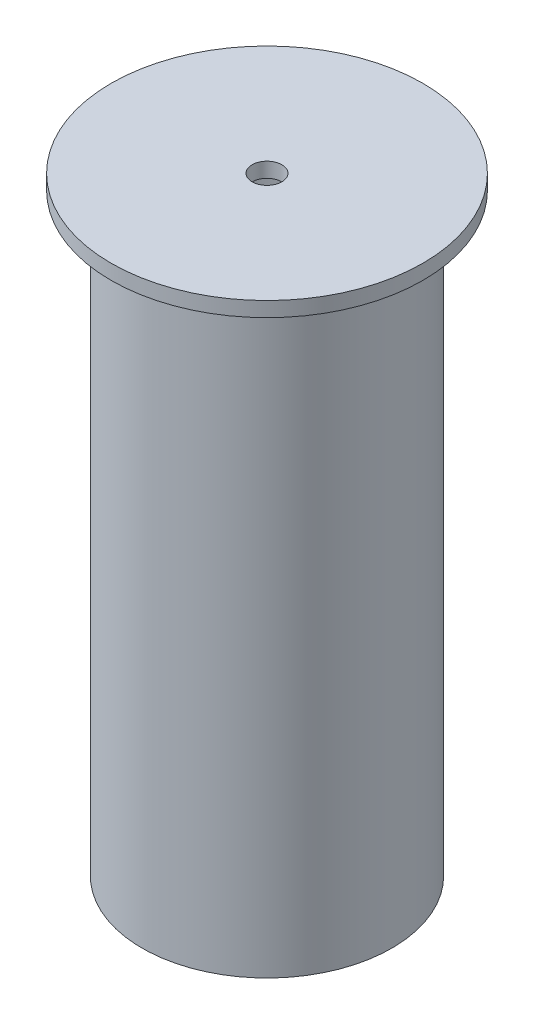
SolidWorks part; units mm, degrees
material "AISI 1020"
ref_plane "Plano frontal" through (0, 0, 0) normal (0, 0, 1) x (1, 0, 0)
ref_plane "Plano superior" through (0, 0, 0) normal (0, 1, 0) x (1, 0, 0)
ref_plane "Plano direito" through (0, 0, 0) normal (1, 0, 0) x (0, 0, -1)
sketch "Esboço1" plane through (0, 0, 0) normal (0, 0, 1) x (1, 0, 0)
  line L0 (0, 0) -> (0, 410) construction
  line L1 (0, 0) -> (215.8131, 0) construction
  line L2 (10, 410) -> (105, 410)
  line L3 (105, 410) -> (105, 400)
  line L4 (84.14, 0) -> (74.74, 0)
  line L5 (74.74, 0) -> (74.74, 10)
  line L6 (74.74, 10) -> (80.74, 10)
  line L7 (80.74, 10) -> (80.74, 400)
  line L8 (80.74, 400) -> (10, 400)
  line L10 (105, 400) -> (84.14, 400)
  line L11 (84.14, 400) -> (84.14, 0)
  line L12 (10, 410) -> (10, 400)
  dimension "D1" = 3.4
  dimension "D2" = 10
  dimension "D3" = 6
  dimension "D4" = 10
  dimension "D5" = 210
  dimension "D6" = 400
  dimension "D7" = 168.28
  dimension "D8" = 20
revolve "Revolução1" add sketch "Esboço1" angle 360 about L0
